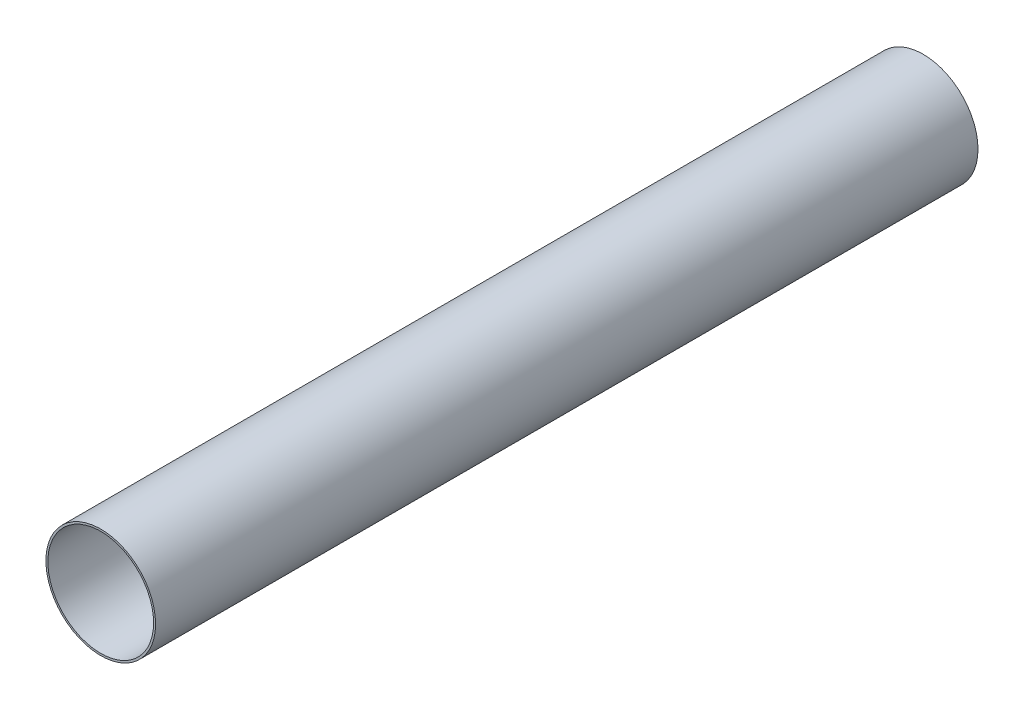
SolidWorks part; units mm, degrees
ref_plane "Front" through (0, 0, 0) normal (0, 0, 1) x (1, 0, 0)
ref_plane "Top" through (0, 0, 0) normal (0, 1, 0) x (1, 0, 0)
ref_plane "Side" through (0, 0, 0) normal (1, 0, 0) x (0, 0, -1)
sketch "PipeSketch" plane through (0, 0, 0) normal (0, 0, 1) x (1, 0, 0)
  circle A0 centre (0, 0) radius 177.8
  circle A1 centre (0, 0) radius 171.45
  dimension "OuterDiameter" = 355.6
  dimension "InnerDiameter" = 342.9
extrude "Extrusion" add sketch "PipeSketch" along normal blind 2666.6
sketch "FilterSketch" plane through (0, 0, 0) normal (0, 0, 1) x (1, 0, 0)
  circle A0 centre (0, 0) radius 177.8 construction
  dimension "NominalDiameter" = 355.6
